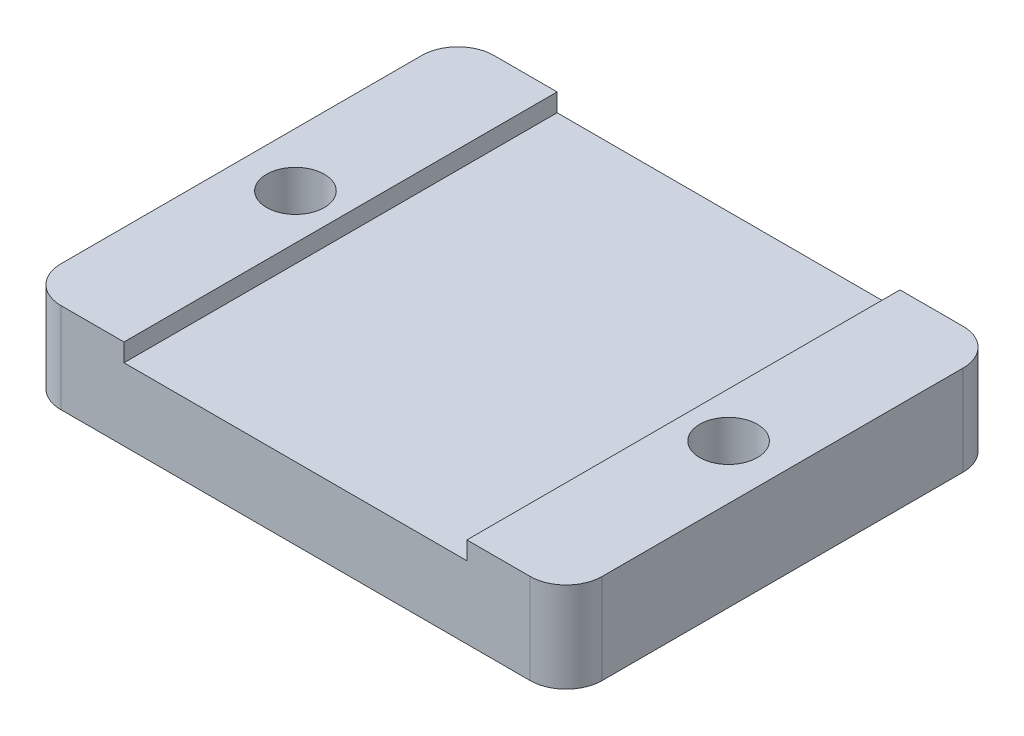
SolidWorks part; units mm, degrees
ref_plane "前视基准面" through (0, 0, 0) normal (0, 0, 1) x (1, 0, 0)
ref_plane "上视基准面" through (0, 0, 0) normal (0, 1, 0) x (1, 0, 0)
ref_plane "右视基准面" through (0, 0, 0) normal (1, 0, 0) x (0, 0, -1)
sketch "草图1" plane through (0, 0, 0) normal (0, 1, 0) x (1, 0, 0)
  line L1 (-15, 12) -> (15, 12)
  line L2 (-15, 12) -> (-15, -12)
  line L3 (-15, -12) -> (15, -12)
  line L4 (15, 12) -> (15, -12)
  line L5 (0, -12) -> (0, 12) construction
  line L6 (-15, 0) -> (15, 0) construction
  circle A0 centre (-12, 0) radius 1.6
  circle A2 centre (12, 0) radius 1.6
  point P0 (0, 0)
  dimension "D3" = 3.2
  dimension "D4" = 12
  dimension "D1" = 30
  dimension "D2" = 24
extrude "凸台-拉伸1" add sketch "草图1" along normal blind 4
sketch "草图2" plane through (0, 4, 0) normal (0, 1, 0) x (1, 0, 0)
  line L0 (0, 21.1964) -> (0, -17.8497) construction
  line L1 (-9.5, 12) -> (-9.5, -12)
  line L2 (9.5, 12) -> (9.5, -12)
  line L3 (-15, -12) -> (15, -12) construction
  line L5 (-15, 12) -> (-9.5, 12)
  line L6 (-15, 12) -> (-15, -12)
  line L7 (-15, -12) -> (-9.5, -12)
  line L8 (-9.5, 12) -> (-9.5, -12)
  line L10 (15, 12) -> (9.5, 12)
  line L11 (15, 12) -> (15, -12)
  line L12 (15, -12) -> (9.5, -12)
  line L13 (9.5, 12) -> (9.5, -12)
  circle A0 centre (12, 0) radius 1.6 construction
  circle A1 centre (-12, 0) radius 1.6 construction
  circle A2 centre (12, 0) radius 1.6
  circle A3 centre (-12, 0) radius 1.6
  circle M5 centre (-12, 0) radius 1.6
  line M6 (15, -12) -> (15, 12)
  line M7 (15, 12) -> (-15, 12)
  line M8 (-15, 12) -> (-15, -12)
  line M9 (-15, -12) -> (15, -12)
  circle M10 centre (12, 0) radius 1.6
  dimension "D1" = 9.5
  dimension "D2" = 9.5
extrude "凸台-拉伸2" add sketch "草图2" along normal blind 1 contours L1 M7 M8 M9 M5 | L2 M7 M9 M6 M10
fillet "圆角1" radius 2 4 edges at (15, 2.5, -12) (15, 2.5, 12) (-15, 2.5, 12) (-15, 2.5, -12)
